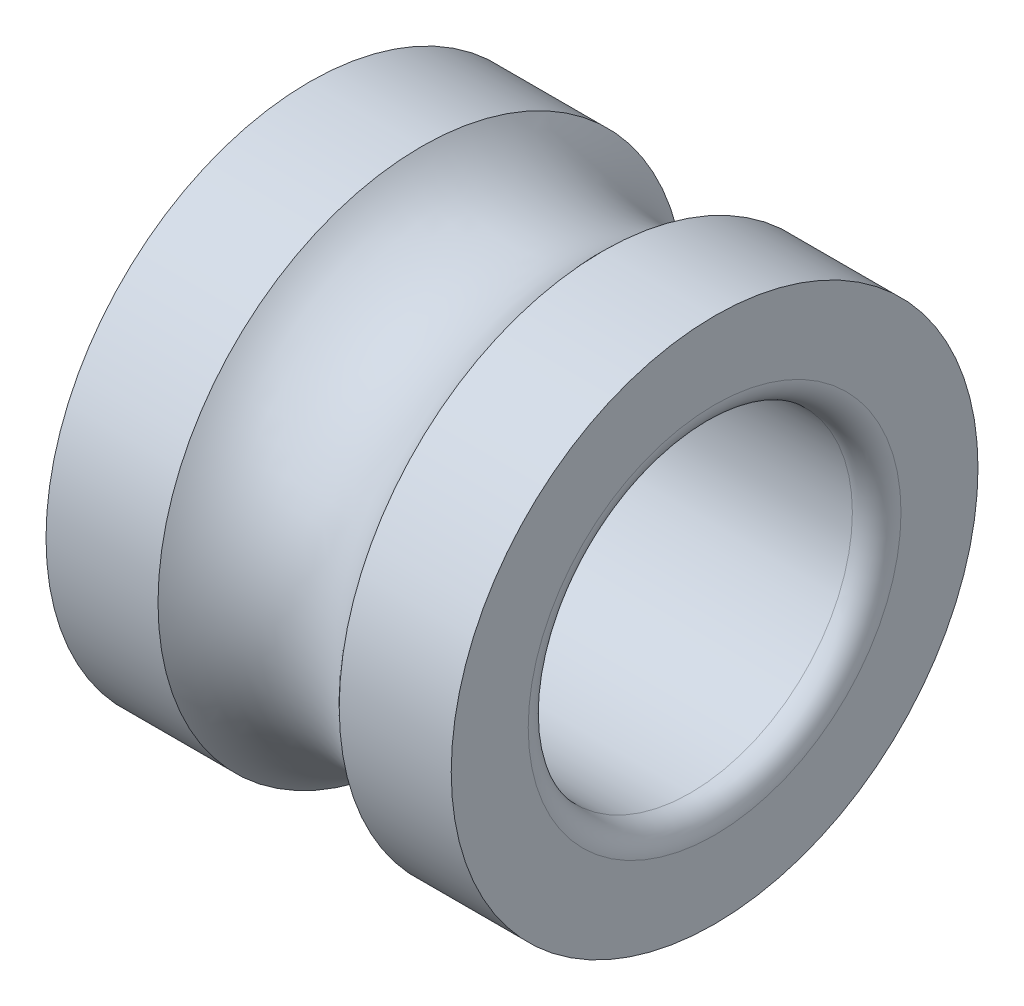
SolidWorks part; units mm, degrees
ref_plane "Plan1" through (0, 0, 0) normal (0, 0, 1) x (1, 0, 0)
ref_plane "Plan2" through (0, 0, 0) normal (0, 1, 0) x (1, 0, 0)
ref_plane "Plan3" through (0, 0, 0) normal (1, 0, 0) x (0, 0, -1)
sketch "Esquisse1" plane through (0, 0, 0) normal (0, 0, 1) x (1, 0, 0)
  line L0 (3.618, 3.25) -> (5, 3.25) construction
  line L1 (0, 2) -> (0, 3.25) construction
  line L2 (0, 3.25) -> (1.382, 3.25) construction
  line L3 (5, 2) -> (5, 3.25) construction
  line L4 (0, 2) -> (5, 2) construction
  line L5 (3.618, 3.25) -> (5, 3.25)
  line L6 (0, 2) -> (0, 3.25)
  line L7 (0, 3.25) -> (1.382, 3.25)
  line L8 (5, 2) -> (5, 3.25)
  line L9 (0, 2) -> (5, 2)
  line L10 (0, 0) -> (11.4296, 0) construction
  line L11 (0, 0) -> (24.3288, 0) construction
  circle A0 centre (2.5, 4.25) radius 1.5 construction
  arc A1 (1.382, 3.25) -> (3.618, 3.25) centre (2.5, 4.25) ccw
revolve "Base-Révolution" add sketch "Esquisse1" angle 360 about L10
fillet "Congé1" radius 0.3
